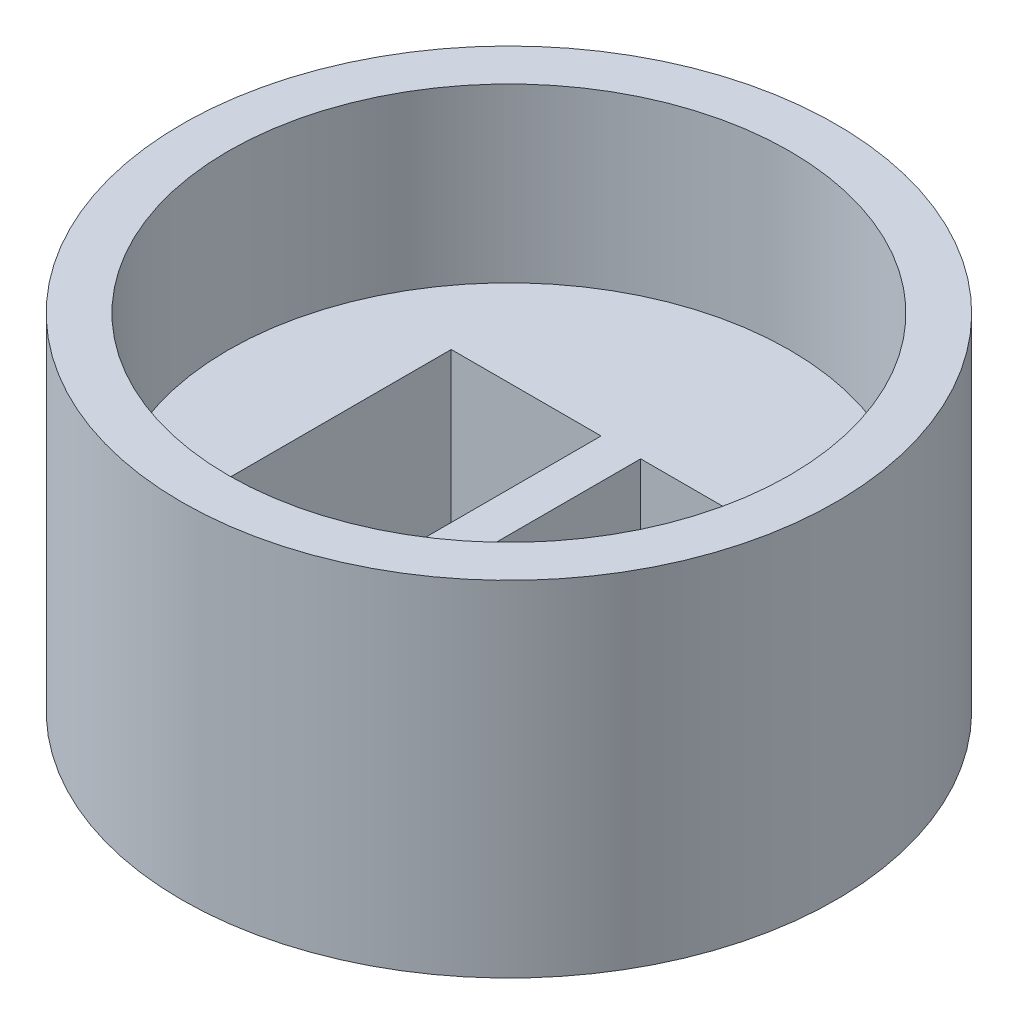
SolidWorks part; units mm, degrees
ref_plane "Front Plane" through (0, 0, 0) normal (0, 0, 1) x (1, 0, 0)
ref_plane "Top Plane" through (0, 0, 0) normal (0, 1, 0) x (1, 0, 0)
ref_plane "Right Plane" through (0, 0, 0) normal (1, 0, 0) x (0, 0, -1)
sketch "Sketch2" plane through (0, 0, 0) normal (0, 1, 0) x (1, 0, 0)
  circle A0 centre (0, 0) radius 9.5
  dimension "D1" = 19
extrude "Boss-Extrude2" add sketch "Sketch2" along normal blind 10
sketch "Sketch3" plane through (0, 10, 0) normal (0, 1, 0) x (1, 0, 0)
  circle A0 centre (0, 0) radius 8.15
  dimension "D1" = 16.3
extrude "Cut-Extrude1" cut sketch "Sketch3" against normal blind 5
sketch "Sketch4" plane through (0, 5, 0) normal (0, 1, 0) x (1, 0, 0)
  line L0 (-8.15, 0) -> (8.15, 0) construction
  line L2 (4.925, -3.25) -> (0.575, -3.25)
  line L3 (4.925, -3.25) -> (4.925, 3.25)
  line L4 (4.925, 3.25) -> (0.575, 3.25)
  line L5 (0.575, -3.25) -> (0.575, 3.25)
  line L6 (4.925, -3.25) -> (0.575, 3.25) construction
  line L7 (4.925, 3.25) -> (0.575, -3.25) construction
  line L8 (-4.925, 3.25) -> (-0.575, 3.25)
  line L9 (-4.925, 3.25) -> (-4.925, -3.25)
  line L10 (-4.925, -3.25) -> (-0.575, -3.25)
  line L11 (-0.575, 3.25) -> (-0.575, -3.25)
  line L12 (-4.925, 3.25) -> (-0.575, -3.25) construction
  line L13 (-4.925, -3.25) -> (-0.575, 3.25) construction
  circle A0 centre (0, 0) radius 8.15 construction
  circle A1 centre (0, 0) radius 8.15 construction
  point P7 (2.75, 0)
  point P12 (-2.75, 0)
  dimension "D1" = 4.35
  dimension "D2" = 6.5
  dimension "D3" = 4.35
  dimension "D4" = 6.5
  dimension "D5" = 2.75
  dimension "D6" = 2.75
extrude "Cut-Extrude2" cut sketch "Sketch4" against normal through all
